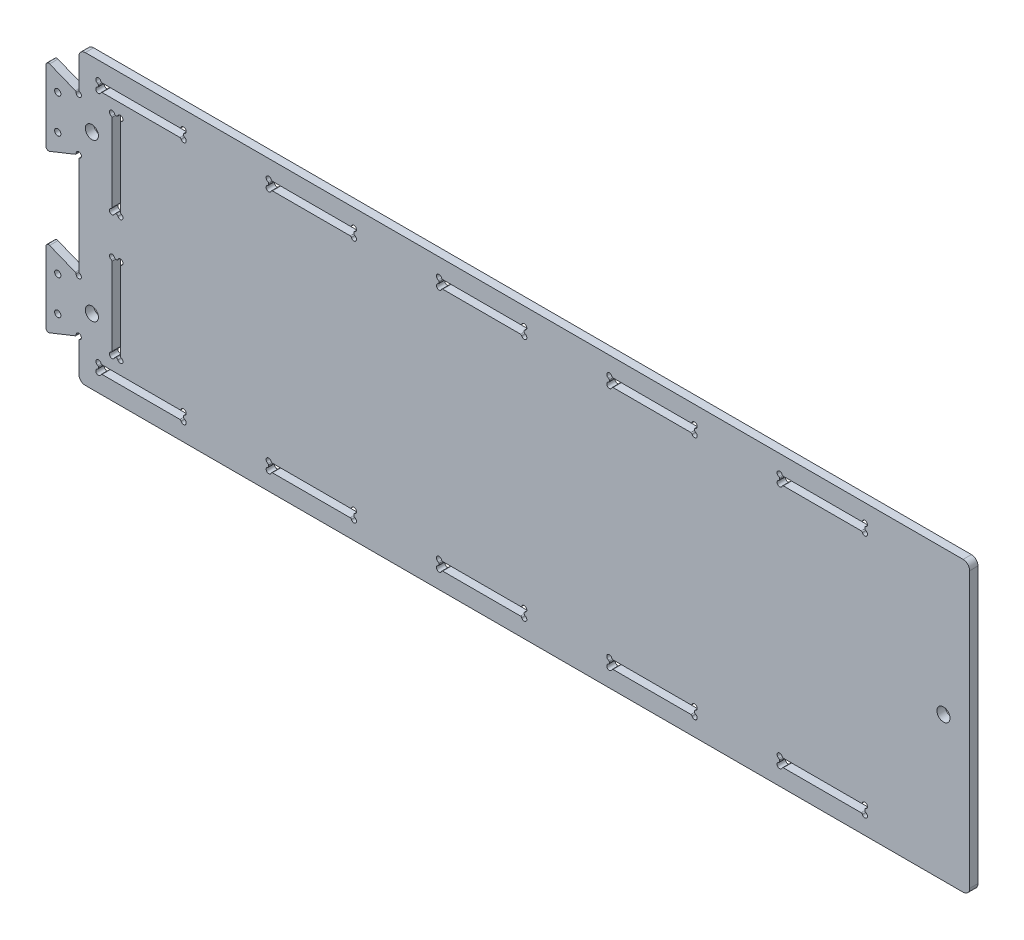
SolidWorks part; units mm, degrees
material "Pine"
ref_plane "Front Plane" through (0, 0, 0) normal (0, 0, 1) x (1, 0, 0)
ref_plane "Top Plane" through (0, 0, 0) normal (0, 1, 0) x (1, 0, 0)
ref_plane "Right Plane" through (0, 0, 0) normal (1, 0, 0) x (0, 0, -1)
sketch "Sketch1" plane through (0, 0, 0) normal (0, 0, 1) x (1, 0, 0)
  line L0 (0, 0) -> (680, 0)
  line L1 (0, 0) -> (0, 220)
  line L2 (680, 0) -> (680, 220)
  line L3 (0, 220) -> (680, 220)
  dimension "D1" = 680
  dimension "D2" = 220
extrude "Boss-Extrude1" add sketch "Sketch1" along normal mid plane 6.35
ref_plane "Plane1" through (0, 110, 0) normal (0, 1, 0) x (1, 0, 0)
sketch "Sketch2" plane through (0, 0, 3.175) normal (0, 0, 1) x (1, 0, 0)
  line L0 (535, 206.35) -> (600, 206.35)
  line L1 (535, 206.35) -> (535, 200)
  line L2 (600, 206.35) -> (600, 200)
  line L3 (535, 200) -> (600, 200)
  line L4 (680, 0) -> (680, 220) construction
  line L5 (680, 110) -> (0, 110) construction
  line L6 (0, 220) -> (0, 0) construction
  dimension "D1" = 80
  dimension "D2" = 96.35
  dimension "D3" = 6.35
  dimension "D4" = 65
extrude "Cut-Extrude1" cut sketch "Sketch2" against normal through all
sketch "Sketch3" plane through (0, 0, 3.175) normal (0, 0, 1) x (1, 0, 0)
  circle A0 centre (535, 206.35) radius 2
  circle A1 centre (535, 200) radius 2
  circle A2 centre (600, 200) radius 2
  circle A3 centre (600, 206.35) radius 2
  dimension "D1" = 4
extrude "Cut-Extrude2" cut sketch "Sketch3" against normal through all
sketch "Sketch4" plane through (0, 0, 3.175) normal (0, 0, 1) x (1, 0, 0)
  line L0 (537, 200) -> (598, 200) construction
  line L1 (600, 202) -> (600, 204.35) construction
  line L2 (598, 206.35) -> (537, 206.35) construction
  line L3 (535, 204.35) -> (535, 202) construction
  line L4 (537.8284, 200) -> (597.1716, 200)
  line L5 (600, 202.8284) -> (600, 203.5216)
  line L6 (597.1716, 206.35) -> (537.8284, 206.35)
  line L7 (535, 203.5216) -> (535, 202.8284)
  arc A0 (598, 200) -> (600, 202) centre (600, 200) ccw construction
  arc A1 (600, 204.35) -> (598, 206.35) centre (600, 206.35) ccw construction
  arc A2 (537, 206.35) -> (535, 204.35) centre (535, 206.35) ccw construction
  arc A3 (535, 202) -> (537, 200) centre (535, 200) ccw construction
  arc A4 (598.1144, 199.3333) -> (600.6667, 201.8856) centre (600, 200) ccw
  arc A5 (600.6667, 204.4644) -> (598.1144, 207.0167) centre (600, 206.35) ccw
  arc A6 (536.8856, 207.0167) -> (534.3333, 204.4644) centre (535, 206.35) ccw
  arc A7 (534.3333, 201.8856) -> (536.8856, 199.3333) centre (535, 200) ccw
  arc A8 (597.1716, 200) -> (598.1144, 199.3333) centre (597.1716, 199) cw
  arc A9 (600.6667, 201.8856) -> (600, 202.8284) centre (601, 202.8284) cw
  arc A10 (600, 203.5216) -> (600.6667, 204.4644) centre (601, 203.5216) cw
  arc A11 (598.1144, 207.0167) -> (597.1716, 206.35) centre (597.1716, 207.35) cw
  arc A12 (537.8284, 206.35) -> (536.8856, 207.0167) centre (537.8284, 207.35) cw
  arc A13 (534.3333, 204.4644) -> (535, 203.5216) centre (534, 203.5216) cw
  arc A14 (535, 202.8284) -> (534.3333, 201.8856) centre (534, 202.8284) cw
  arc A15 (536.8856, 199.3333) -> (537.8284, 200) centre (537.8284, 199) cw
  dimension "D1" = 1
extrude "Cut-Extrude3" cut sketch "Sketch4" against normal through all
pattern_linear "LPattern1" count 5 spacing 130 along (-1, 0, 0) of "Cut-Extrude3"
mirror "Mirror1" about plane through (0, 110, 0) normal (0, 1, 0) of "LPattern1", "Cut-Extrude3"
sketch "Sketch5" plane through (0, 0, 3.175) normal (0, 0, 1) x (1, 0, 0)
  line L0 (31.7633, 94) -> (31.7633, 35) construction
  line L1 (31.7633, 35) -> (25.4133, 35) construction
  line L2 (25.4133, 35) -> (25.4133, 94) construction
  line L3 (25.4133, 94) -> (31.7633, 94) construction
  line L4 (25.4133, 126) -> (25.4133, 185) construction
  line L5 (25.4133, 185) -> (31.7633, 185) construction
  line L6 (31.7633, 185) -> (31.7633, 126) construction
  line L7 (31.7633, 126) -> (25.4133, 126) construction
  line L8 (25.4133, 30) -> (31.7633, 30) construction
  line L9 (31.7633, 95) -> (25.4133, 95) construction
  line L10 (25.4133, 125) -> (31.7633, 125) construction
  line L11 (31.7633, 190) -> (25.4133, 190) construction
  line L12 (31.7633, 94) -> (31.7633, 35) construction
  line L13 (31.7633, 35) -> (25.4133, 35) construction
  line L14 (25.4133, 35) -> (25.4133, 94) construction
  line L15 (25.4133, 94) -> (31.7633, 94) construction
  line L16 (25.4133, 126) -> (25.4133, 185) construction
  line L17 (25.4133, 185) -> (31.7633, 185) construction
  line L18 (31.7633, 185) -> (31.7633, 126) construction
  line L19 (31.7633, 126) -> (25.4133, 126) construction
  line L20 (25.4133, 30) -> (31.7633, 30) construction
  line L21 (31.7633, 95) -> (25.4133, 95) construction
  line L22 (25.4133, 125) -> (31.7633, 125) construction
  line L23 (31.7633, 190) -> (25.4133, 190) construction
  line L24 (31.7633, 30) -> (25.4133, 30)
  line L25 (31.7633, 30) -> (31.7633, 95)
  line L26 (25.4133, 30) -> (25.4133, 95)
  line L27 (31.7633, 95) -> (25.4133, 95)
  line L28 (31.7633, 125) -> (25.4133, 125)
  line L29 (31.7633, 125) -> (31.7633, 190)
  line L30 (25.4133, 125) -> (25.4133, 190)
  line L31 (31.7633, 190) -> (25.4133, 190)
extrude "Cut-Extrude4" cut sketch "Sketch5" against normal through all
sketch "Sketch6" plane through (0, 0, 3.175) normal (0, 0, 1) x (1, 0, 0)
  circle A0 centre (25.4133, 190) radius 2
  circle A1 centre (31.7633, 190) radius 2
  circle A2 centre (31.7633, 125) radius 2
  circle A3 centre (25.4133, 125) radius 2
  circle A4 centre (25.4133, 95) radius 2
  circle A5 centre (31.7633, 95) radius 2
  circle A6 centre (25.4133, 30) radius 2
  circle A7 centre (31.7633, 30) radius 2
  dimension "D1" = 4
extrude "Cut-Extrude5" cut sketch "Sketch6" against normal through all
fillet "Fillet1" radius 1 16 edges at (29.7633, 190, 0) (27.4133, 190, 0) (25.4133, 188, 0) (31.7633, 188, 0) (31.7633, 127, 0) (29.7633, 125, 0) (27.4133, 125, 0) (25.4133, 127, 0) (25.4133, 93, 0) (27.4133, 95, 0) (29.7633, 95, 0) (31.7633, 93, 0) (31.7633, 32, 0) (29.7633, 30, 0) (27.4133, 30, 0) (25.4133, 32, 0)
sketch "Sketch7" plane through (0, 0, 3.175) normal (0, 0, 1) x (1, 0, 0)
  line L0 (0, 190) -> (-25, 200)
  line L1 (0, 220) -> (0, 0) construction
  line L2 (-25, 200) -> (-25, 140)
  line L3 (-25, 140) -> (0, 150)
  line L4 (0, 70) -> (-25, 80)
  line L5 (-25, 80) -> (-25, 20)
  line L6 (-25, 20) -> (0, 30)
  line L7 (0, 70) -> (0, 30)
  line L8 (0, 50) -> (-25, 50) construction
  line L9 (0, 190) -> (0, 150)
  line L10 (0, 110) -> (680, 110) construction
  line L11 (680, 0) -> (680, 220) construction
  line L12 (0, 110) -> (0, 50) construction
  line L13 (0, 110) -> (0, 170) construction
  dimension "D1" = 25
  dimension "D2" = 40
  dimension "D3" = 60
  dimension "D4" = 120
extrude "Boss-Extrude2" add sketch "Sketch7" against normal up to surface (6.35 mm away) up to face at (28.5883, 157.5, -3.175)
sketch "Sketch8" plane through (0, 0, 3.175) normal (0, 0, 1) x (1, 0, 0)
  circle A0 centre (0, 190) radius 2
  circle A1 centre (0, 150) radius 2
  circle A2 centre (0, 70) radius 2
  circle A3 centre (0, 30) radius 2
  dimension "D1" = 4
extrude "Cut-Extrude6" cut sketch "Sketch8" against normal through all
sketch "Sketch10" plane through (0, 0, -3.175) normal (0, 0, -1) x (-1, 0, 0)
  line L4 (-10, 170) -> (-10, 50) construction
  line L5 (0, 110) -> (-10, 110) construction
  line L6 (0, 148) -> (0, 72) construction
  line L7 (-660, 220) -> (-660, 0) construction
  line L8 (-680, 220) -> (0, 220) construction
  line L9 (0, 0) -> (-680, 0) construction
  line L10 (-680, 0) -> (-680, 220) construction
  circle A1 centre (-10, 170) radius 5
  circle A2 centre (-10, 50) radius 5
  circle A3 centre (-660, 110) radius 5
  dimension "D2" = 10
  dimension "D1" = 10
  dimension "D3" = 120
  dimension "D4" = 20
extrude "Cut-Extrude9" cut sketch "Sketch10" against normal through all
fillet "Fillet2" radius 1 8 edges at (0, 192, 0) (-1.857, 190.7428, 0) (-1.857, 149.2572, 0) (0, 148, 0) (-1.857, 70.7428, 0) (0, 72, 0) (-1.857, 29.2572, 0) (0, 28, 0)
fillet "Fillet3" radius 2 4 edges at (-25, 200, 0) (-25, 140, 0) (-25, 80, 0) (-25, 20, 0)
fillet "Fillet4" radius 5 4 edges at (680, 0, 0) (680, 220, 0) (0, 220, 0) (0, 0, 0)
sketch "Sketch9" plane through (0, 0, -3.175) normal (0, 0, -1) x (-1, 0, 0)
  line L0 (16.0491, 36.7902) -> (16.0491, 23.5804) construction
  line L1 (22.2572, 21.0971) -> (2.6261, 28.9495) construction
  line L2 (16.0491, 36.7902) -> (16.0491, 50) construction
  line L3 (16.0491, 50) -> (16.0491, 63.2098) construction
  line L4 (16.0491, 63.2098) -> (16.0491, 76.4196) construction
  line L6 (2.6261, 71.0505) -> (22.2572, 78.9029) construction
  circle A0 centre (16.0491, 36.7902) radius 2.38
  circle A1 centre (16.0491, 63.2098) radius 2.38
  dimension "D1" = 4.76
  dimension "D2" = 26.4196
ref_plane "Plane2" through (0, 110, 0) normal (0, -1, 0) x (-1, 0, 0)
extrude "Cut-Extrude8" cut sketch "Sketch9" against normal up to surface (6.35 mm away) up to face at (5, 170, 3.175)
mirror "Mirror2" about plane through (0, 110, 0) normal (0, -1, 0) of "Cut-Extrude8"
